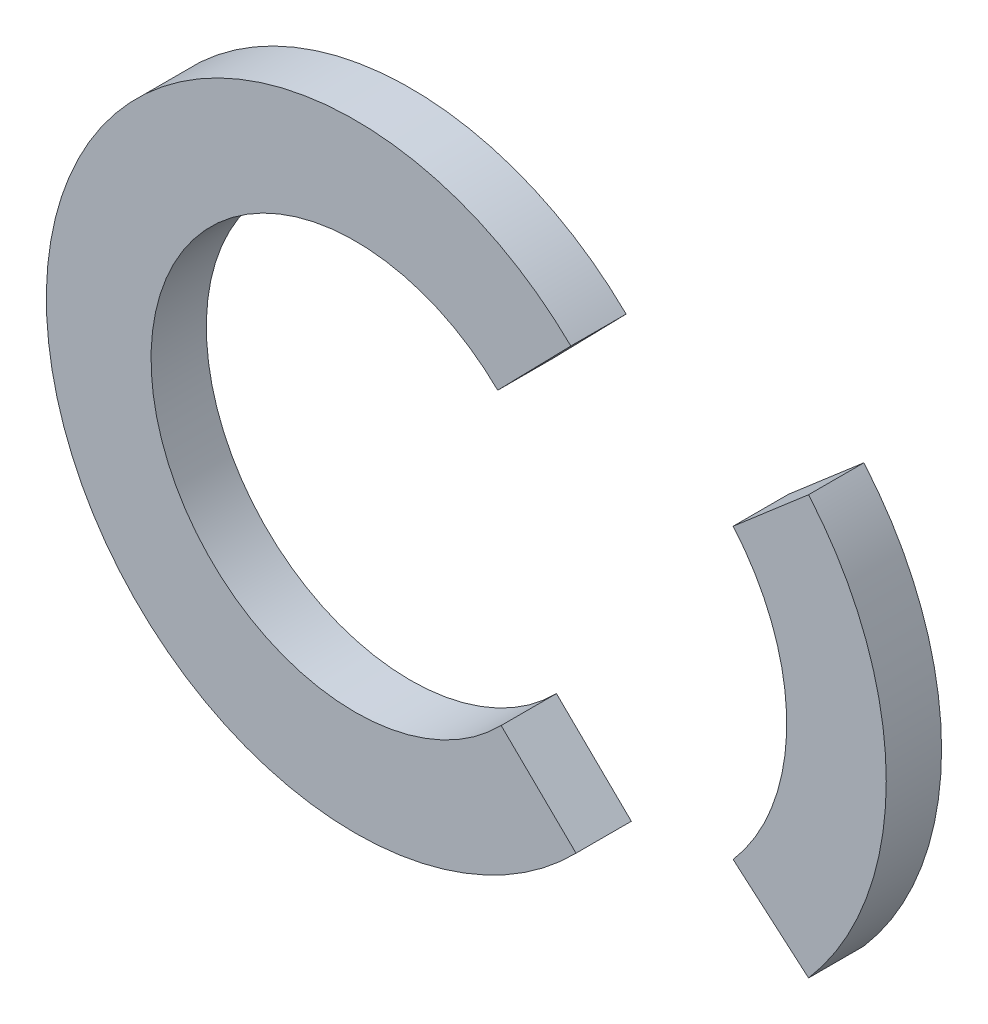
SolidWorks part; units mm, degrees
ref_plane "Plan de face" through (0, 0, 0) normal (0, 0, 1) x (1, 0, 0)
ref_plane "Plan de dessus" through (0, 0, 0) normal (0, 1, 0) x (1, 0, 0)
ref_plane "Plan de droite" through (0, 0, 0) normal (1, 0, 0) x (0, 0, -1)
sketch "Esquisse1" plane through (0, 0, 0) normal (0, 0, 1) x (1, 0, 0)
  line L0 (39.0162, 39.9544) -> (25.7889, 26.4091)
  line L1 (26.4091, -25.7889) -> (39.9544, -39.0162)
  line L2 (82.008, 38.1584) -> (68.3715, 26.4091)
  line L3 (68.3715, -25.7889) -> (82.008, -37.5383)
  arc A0 (39.0162, 39.9544) -> (39.9544, -39.0162) centre (0, 0) ccw
  arc A1 (25.7889, 26.4091) -> (26.4091, -25.7889) centre (0, 0) ccw
  arc A2 (68.3715, 26.4091) -> (68.3715, -25.7889) centre (38.0805, 0.3101) cw
  arc A3 (82.008, 38.1584) -> (82.008, -37.5383) centre (38.0805, 0.3101) cw
  dimension "D1" = 18
extrude "Boss.-Extru.1" add sketch "Esquisse1" along normal blind 10
